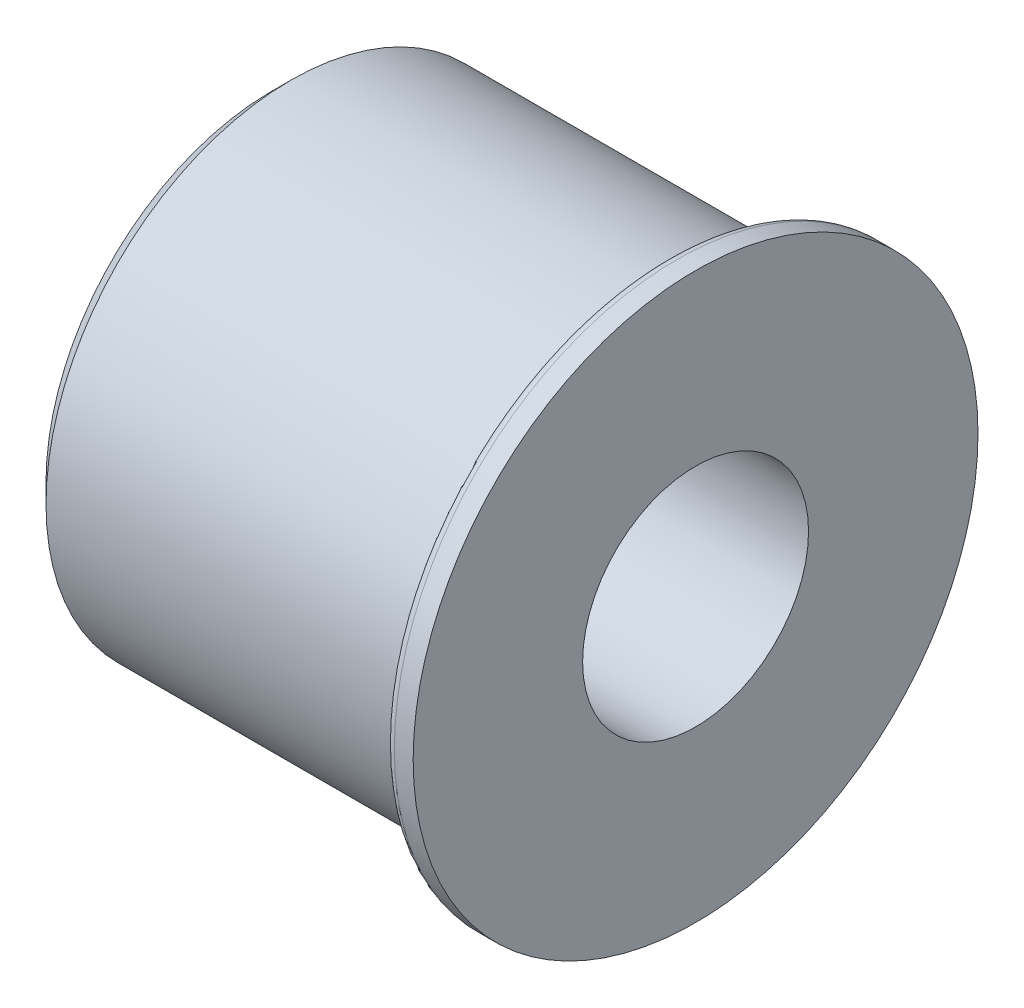
SolidWorks part; units mm, degrees
ref_plane "Plan de face" through (0, 0, 0) normal (0, 0, 1) x (1, 0, 0)
ref_plane "Plan de dessus" through (0, 0, 0) normal (0, 1, 0) x (1, 0, 0)
ref_plane "Plan de droite" through (0, 0, 0) normal (1, 0, 0) x (0, 0, -1)
sketch "Esquisse1" plane through (0, 0, 0) normal (0, 0, 1) x (1, 0, 0)
  line L0 (0, 0) -> (20.7387, 0) construction
  line L3 (0, 6) -> (22.5, 6)
  line L4 (0, 6) -> (0, 12)
  line L5 (22.5, 6) -> (22.5, 15)
  line L6 (22.5, 15) -> (21.5, 15)
  line L7 (21, 14.5) -> (21, 13)
  line L8 (1, 13) -> (21, 13)
  line L9 (0, 12) -> (1, 13)
  arc A0 (21.5, 15) -> (21, 14.5) centre (21.5, 14.5) ccw
  point P3 (0, 13)
  dimension "D1" = 0.5
  dimension "D2" = 6
  dimension "D3" = 15
  dimension "D5" = 22.5
  dimension "D6" = 1.5
revolve "Révolution1" add sketch "Esquisse1" angle 360 about L0
